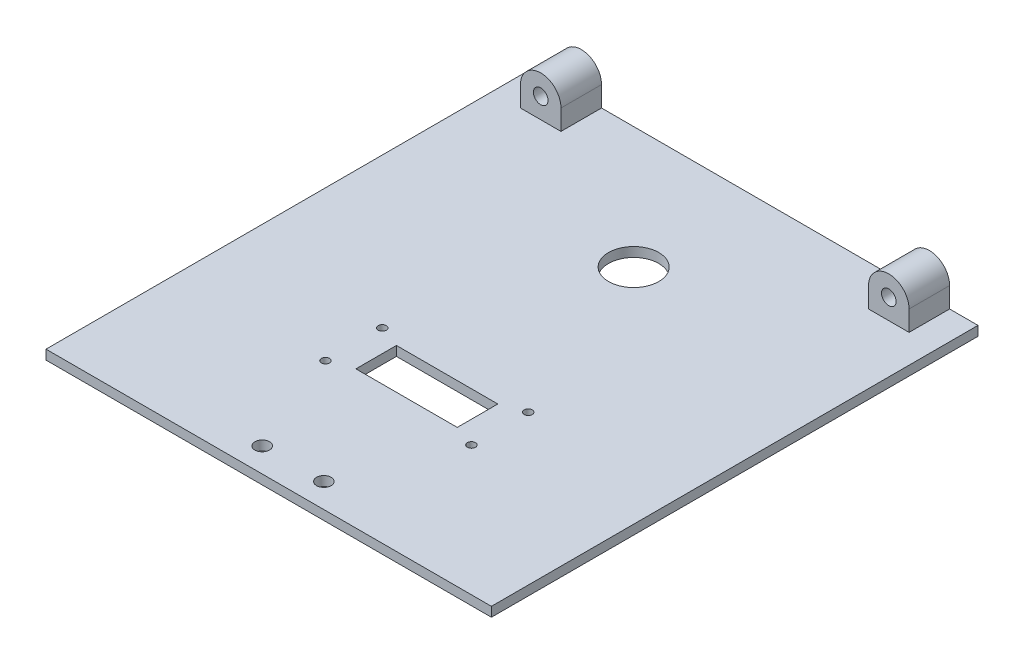
SolidWorks part; units mm, degrees
ref_plane "Front Plane" through (0, 0, 0) normal (0, 0, 1) x (1, 0, 0)
ref_plane "Top Plane" through (0, 0, 0) normal (0, 1, 0) x (1, 0, 0)
ref_plane "Right Plane" through (0, 0, 0) normal (1, 0, 0) x (0, 0, -1)
sketch "Sketch1" plane through (0, 0, 0) normal (0, 1, 0) x (1, 0, 0)
  line L1 (0, 0) -> (139.5, 0)
  line L2 (0, 0) -> (0, 152.4)
  line L3 (0, 152.4) -> (139.5, 152.4)
  line L4 (139.5, 0) -> (139.5, 152.4)
  dimension "D1" = 152.4
  dimension "D2" = 139.5
extrude "Boss-Extrude1" add sketch "Sketch1" along normal blind 6.35
sketch "Sketch2" plane through (0, 6.35, 0) normal (0, 1, 0) x (1, 0, 0)
  line L0 (0, 0) -> (139.5, 0) construction
  line L1 (0, 152.4) -> (139.5, 152.4)
  line L2 (0, 152.4) -> (0, 0)
  line L3 (0, 0) -> (139.5, 0)
  line L4 (139.5, 152.4) -> (139.5, 0)
  line L5 (139.5, 0) -> (139.5, 152.4) construction
extrude "Cut-Extrude1" cut sketch "Sketch2" against normal blind 3.375
sketch "Sketch4" plane through (0, 0, -152.4) normal (0, 0, -1) x (-1, 0, 0)
  line L0 (-130.61, 9.325) -> (-130.61, 2.975)
  line L1 (-130.61, 2.975) -> (-117.91, 2.975)
  line L2 (-117.91, 9.325) -> (-117.91, 2.975)
  line L3 (-21.59, 9.325) -> (-21.59, 2.975)
  line L4 (-21.59, 2.975) -> (-8.89, 2.975)
  line L5 (-8.89, 9.325) -> (-8.89, 2.975)
  line L6 (-139.5, 2.975) -> (0, 2.975) construction
  line L7 (0, 2.975) -> (0, 0) construction
  line L8 (-139.5, 2.975) -> (-139.5, 0) construction
  arc A0 (-117.91, 9.325) -> (-130.61, 9.325) centre (-124.26, 9.325) ccw
  circle A1 centre (-124.26, 9.325) radius 2.286
  arc A2 (-8.89, 9.325) -> (-21.59, 9.325) centre (-15.24, 9.325) ccw
  circle A3 centre (-15.24, 9.325) radius 2.286
  dimension "D1" = 4.572
  dimension "D3" = 6.35
  dimension "D5" = 4.572
  dimension "D7" = 6.35
  dimension "D2" = 6.35
  dimension "D4" = 12.7
  dimension "D6" = 6.35
  dimension "D8" = 12.7
  dimension "D9" = 8.89
  dimension "D10" = 8.89
  dimension "D11" = 15.24
  dimension "D12" = 15.24
extrude "Boss-Extrude3" add sketch "Sketch4" against normal blind 12.7
sketch "Sketch5" plane through (0, 0, 0) normal (0, -1, 0) x (1, 0, 0)
  line L0 (139.5, -152.4) -> (0, -152.4) construction
  circle A0 centre (69.75, -114.3) radius 7.874
  point P4 (69.75, -152.4)
  dimension "D1" = 15.748
  dimension "D2" = 38.1
extrude "Cut-Extrude2" cut sketch "Sketch5" against normal through all
sketch "Sketch6" plane through (0, 2.975, 0) normal (0, 1, 0) x (1, 0, 0)
  line L0 (0, 0) -> (139.5, 0) construction
  line L2 (69.75, 152.4) -> (69.75, 0) construction
  line L3 (117.91, 152.4) -> (21.59, 152.4) construction
  circle A0 centre (60.098, 7.62) radius 2.286
  circle A1 centre (79.402, 7.62) radius 2.286
  dimension "D3" = 4.572
  dimension "D4" = 7.62
  dimension "D1" = 9.652
  dimension "D2" = 9.652
  dimension "D6" = 7.62
extrude "Cut-Extrude3" cut sketch "Sketch6" against normal through all
sketch "Sketch7" plane through (0, 0, 0) normal (0, -1, 0) x (1, 0, 0)
  line L0 (44.35, -38.1) -> (44.35, -60.96) construction
  line L1 (44.35, -60.96) -> (95.15, -60.96) construction
  line L2 (95.15, -60.96) -> (95.15, -38.1) construction
  line L3 (95.15, -38.1) -> (44.35, -38.1) construction
  line L4 (0, 0) -> (139.5, 0) construction
  line L6 (53.875, -43.18) -> (85.625, -43.18)
  line L7 (53.875, -43.18) -> (53.875, -55.88)
  line L8 (53.875, -55.88) -> (85.625, -55.88)
  line L9 (85.625, -43.18) -> (85.625, -55.88)
  circle A0 centre (46.89, -40.64) radius 1.27
  circle A1 centre (92.61, -40.64) radius 1.27
  circle A2 centre (92.61, -58.42) radius 1.27
  circle A3 centre (46.89, -58.42) radius 1.27
  point P2 (69.75, -38.1)
  point P7 (69.75, 0)
  point P17 (85.625, -49.53)
  point P21 (95.15, -49.53)
  point P22 (69.75, -55.88)
  point P23 (69.75, -60.96)
  dimension "D4" = 2.54
  dimension "D1" = 50.8
  dimension "D2" = 22.86
  dimension "D3" = 38.1
  dimension "D5" = 2.54
  dimension "D6" = 2.54
  dimension "D7" = 17.78
  dimension "D8" = 2.54
  dimension "D9" = 12.7
  dimension "D10" = 31.75
extrude "Cut-Extrude4" cut sketch "Sketch7" against normal through all and the other way through all
